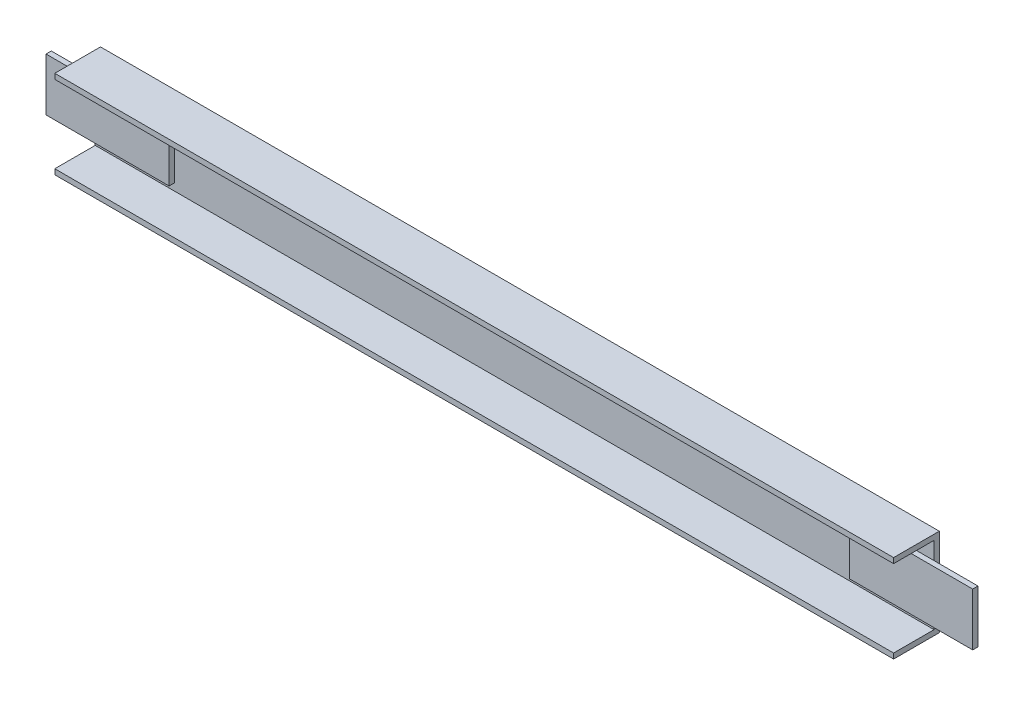
SolidWorks part; units mm, degrees
ref_plane "Front Plane" through (0, 0, 0) normal (0, 0, 1) x (1, 0, 0)
ref_plane "Top Plane" through (0, 0, 0) normal (0, 1, 0) x (1, 0, 0)
ref_plane "Right Plane" through (0, 0, 0) normal (1, 0, 0) x (0, 0, -1)
ref_plane "Plane1" through (0, 0, 514) normal (0, 0, 1) x (1, 0, 0)
sketch "Sketch1" plane through (0, 0, 514) normal (0, 0, 1) x (1, 0, 0)
  line L0 (-61, 120) -> (416, 120)
  line L1 (416, 120) -> (416, 170)
  line L2 (416, 170) -> (-61, 170)
  line L3 (-61, 170) -> (-61, 120)
extrude "Boss-Extrude1" add sketch "Sketch1" against normal blind 26
sketch "Sketch2" plane through (-61, 0, 0) normal (-1, 0, 0) x (0, 0, 1)
  line L0 (514, 123) -> (514, 167)
  line L1 (514, 167) -> (491, 167)
  line L2 (491, 167) -> (491, 123)
  line L3 (491, 123) -> (514, 123)
extrude "Cut-Extrude1" cut sketch "Sketch2" against normal through all
sketch "Sketch3" plane through (0, 0, 491) normal (0, 0, 1) x (1, 0, 0)
  line L0 (371, 130) -> (371, 160)
  line L1 (371, 160) -> (471, 160)
  line L2 (471, 160) -> (471, 130)
  line L3 (471, 130) -> (371, 130)
extrude "Boss-Extrude2" add sketch "Sketch3" along normal blind 3
sketch "Sketch4" plane through (0, 0, 491) normal (0, 0, 1) x (1, 0, 0)
  line L0 (-116, 160) -> (-16, 160)
  line L1 (-16, 160) -> (-16, 130)
  line L2 (-16, 130) -> (-116, 130)
  line L3 (-116, 130) -> (-116, 160)
extrude "Boss-Extrude3" add sketch "Sketch4" along normal blind 3
sketch "Sketch5" plane through (0, 0, 488) normal (0, 0, -1) x (-1, 0, 0)
  line L0 (-167.5, 155) -> (-167.5, 135)
  line L1 (-167.5, 135) -> (-187.5, 135)
  line L2 (-187.5, 135) -> (-187.5, 155)
  line L3 (-187.5, 155) -> (-167.5, 155)
extrude "Boss-Extrude4" add sketch "Sketch5" along normal blind 10
other "Move Face8" face at (-116, 145, 492.5) face at (471, 145, 492.5) parameters "D1"=30
other "Move Face9" face at (408, 130, 492.2) face at (-53, 130, 492.2) parameters "D1"=5
other "Move Face10" face at (-53, 160, 492.2) face at (408, 160, 492.2) parameters "D1"=5
other "Move Face11" face at (-53, 155, 492.2) face at (408, 155, 492.2) parameters "D1"=2
other "Move Face12" face at (408, 125, 492.2) face at (-53, 125, 492.2) parameters "D1"=2
